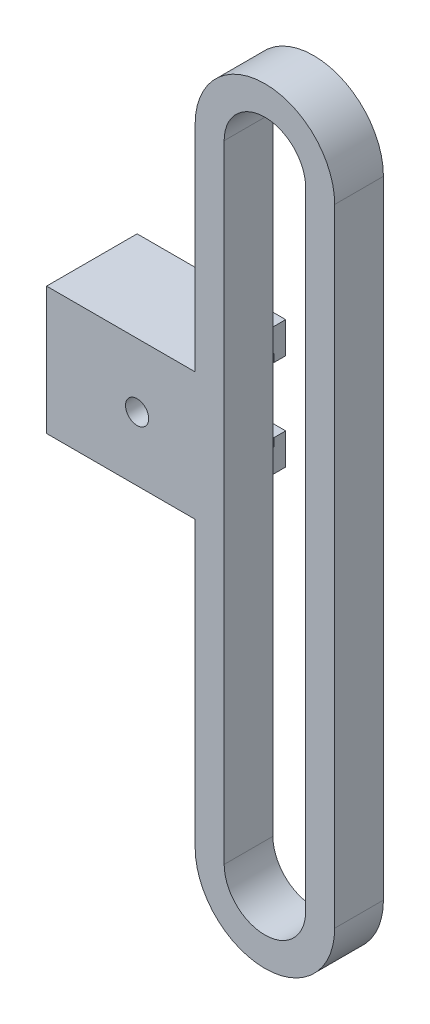
SolidWorks part; units mm, degrees
material "1060 合金"
ref_plane "前视基准面" through (0, 0, 0) normal (0, 0, 1) x (1, 0, 0)
ref_plane "上视基准面" through (0, 0, 0) normal (0, 1, 0) x (1, 0, 0)
ref_plane "右视基准面" through (0, 0, 0) normal (1, 0, 0) x (0, 0, -1)
sketch "草图1" plane through (0, 0, 0) normal (0, 0, 1) x (1, 0, 0)
  line L0 (0, 10.3451) -> (0, -43.6549) construction
  line L1 (3.51, 10.3451) -> (3.51, -43.6549)
  line L2 (-3.51, 10.3451) -> (-3.51, -43.6549)
  line L3 (0, 10.3451) -> (0, -43.6549) construction
  line L4 (6.01, 10.3451) -> (6.01, -43.6549)
  line L5 (-6.01, 10.3451) -> (-6.01, -43.6549)
  arc A0 (3.51, 10.3451) -> (-3.51, 10.3451) centre (0, 10.3451) ccw
  arc A1 (-3.51, -43.6549) -> (3.51, -43.6549) centre (0, -43.6549) ccw
  arc A2 (6.01, 10.3451) -> (-6.01, 10.3451) centre (0, 10.3451) ccw
  arc A3 (-6.01, -43.6549) -> (6.01, -43.6549) centre (0, -43.6549) ccw
  point P3 (0, -16.6549)
  point P8 (0, -16.6549)
  dimension "D2" = 7.02
  dimension "D1" = 54
  dimension "D3" = 2.5
extrude "凸台-拉伸1" add sketch "草图1" along normal blind 4.2
sketch "草图2" plane through (-6.01, 0, 0) normal (-1, 0, 0) x (0, 0, 1)
  line L0 (4.2, -16.6549) -> (4.2, -8.1549)
  line L1 (4.2, -43.6549) -> (4.2, 10.3451) construction
  line L2 (4.2, -8.1549) -> (-2.6, -8.1549)
  line L3 (-2.6, -8.1549) -> (-2.6, -10.1549)
  line L4 (-2.6, -10.1549) -> (2.2, -10.1549)
  line L5 (2.2, -10.1549) -> (2.2, -17.1549)
  line L6 (2.2, -17.1549) -> (-2.6, -17.1549)
  line L7 (-2.6, -17.1549) -> (-2.6, -19.1549)
  line L8 (-2.6, -19.1549) -> (4.2, -19.1549)
  line L9 (4.2, -19.1549) -> (4.2, -16.6549)
  dimension "D1" = 7
  dimension "D2" = 4.8
  dimension "D3" = 4.8
  dimension "D4" = 2
  dimension "D5" = 2
  dimension "D6" = 2
  dimension "D7" = 8.5
extrude "凸台-拉伸2" add sketch "草图2" along normal blind 12.8
sketch "草图3" plane through (0, 0, 2.2) normal (0, 0, -1) x (-1, 0, 0)
  line L0 (6.01, -10.1549) -> (6.01, -17.1549) construction
  line L1 (18.81, -17.1549) -> (6.01, -17.1549) construction
  circle A0 centre (11.01, -13.6549) radius 1
  dimension "D1" = 5
  dimension "D2" = 3.5
  dimension "D3" = 2
extrude "切除-拉伸1" cut sketch "草图3" against normal blind 10
sketch "草图5" plane through (-6.01, 0, 0) normal (1, 0, 0) x (0, 0, -1)
  line L0 (0, -17.1549) -> (2.6, -17.1549) construction
  line L1 (2.6, -8.1549) -> (3.6, -8.1549)
  line L2 (2.6, -8.1549) -> (2.6, -10.8549)
  line L3 (2.6, -10.8549) -> (3.6, -10.8549)
  line L4 (3.6, -8.1549) -> (3.6, -10.8549)
  line L5 (2.6, -19.1549) -> (3.6, -19.1549)
  line L6 (2.6, -19.1549) -> (2.6, -16.4549)
  line L7 (2.6, -16.4549) -> (3.6, -16.4549)
  line L8 (3.6, -19.1549) -> (3.6, -16.4549)
  line L9 (2.6, -10.1549) -> (0, -10.1549) construction
  dimension "D1" = 1
  dimension "D2" = 0.7
  dimension "D3" = 0.7
  dimension "D4" = 1
extrude "凸台-拉伸3" add sketch "草图5" against normal through all
